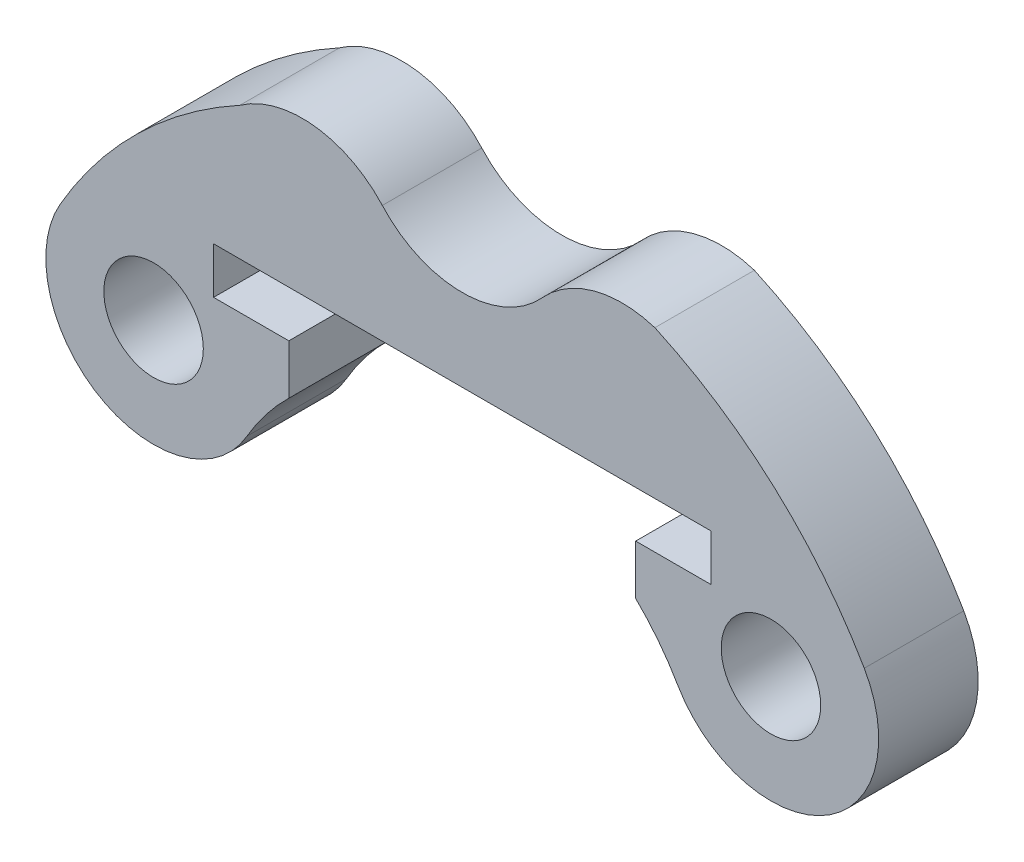
SolidWorks part; units mm, degrees
ref_plane "Plan de face" through (0, 0, 0) normal (0, 0, 1) x (1, 0, 0)
ref_plane "Plan de dessus" through (0, 0, 0) normal (0, 1, 0) x (1, 0, 0)
ref_plane "Plan de droite" through (0, 0, 0) normal (1, 0, 0) x (0, 0, -1)
sketch "Esquisse1" plane through (0, 0, 0) normal (0, 0, 1) x (1, 0, 0)
  line L0 (9.3098, 5.375) -> (7.6848, 2.5604) construction
  line L2 (-9.3098, 5.375) -> (9.3098, 5.375) construction
  line L4 (-7.6848, 2.5604) -> (-9.3098, 5.375) construction
  line L9 (9.3098, 6.875) -> (5.2306, 6.875) construction
  line L11 (-5.2306, 6.875) -> (-7.5, 6.875)
  line L12 (7.5, 6.875) -> (7.5, 8.275)
  line L13 (7.5, 8.275) -> (-7.5, 8.275)
  line L14 (-7.5, 8.275) -> (-7.5, 6.875)
  line L15 (-5.2306, 5.375) -> (-5.2306, 6.875)
  line L16 (5.2306, 5.375) -> (5.2306, 6.875)
  line L17 (-5.2306, 6.875) -> (-9.3098, 6.875) construction
  line L18 (5.2306, 6.875) -> (7.5, 6.875)
  arc A12 (-2.411, 11.8207) -> (2.411, 11.8207) centre (0, 14) ccw
  arc A16 (5.8094, 12.7378) -> (2.411, 11.8207) centre (4.8221, 9.6414) ccw
  arc A17 (-2.411, 11.8207) -> (-6.7074, 12.2887) centre (-4.8221, 9.6414) ccw
  arc A18 (-6.7074, 12.2887) -> (-12.1244, 7) centre (0, 0) ccw
  arc A28 (12.1244, 7) -> (5.8094, 12.7378) centre (0, 0) ccw
  arc A30 (10.4906, 2.3471) -> (-10.4906, 2.3471) centre (0, 0) ccw construction
  circle A31 centre (9.3098, 5.375) radius 1.5
  circle A33 centre (-9.3098, 5.375) radius 1.5
  arc A34 (6.4952, 3.75) -> (12.1244, 7) centre (9.3098, 5.375) ccw
  arc A35 (-12.1244, 7) -> (-6.4952, 3.75) centre (-9.3098, 5.375) ccw
  arc A37 (6.4952, 3.75) -> (5.2306, 5.375) centre (0, 0) ccw
  arc A38 (-5.2306, 5.375) -> (-6.4952, 3.75) centre (0, 0) ccw
  point P31 (0, 0)
  dimension "D3" = 6.5
  dimension "D5" = 1.4
  dimension "D8" = 14
  dimension "D9" = 3.25
  dimension "D10" = 6.5
  dimension "D11" = 3.25
  dimension "D7" = 60
  dimension "D14" = 10.78
  dimension "D15" = 10.78
extrude "Boss.-Extru.2" add sketch "Esquisse1" along normal blind 3
